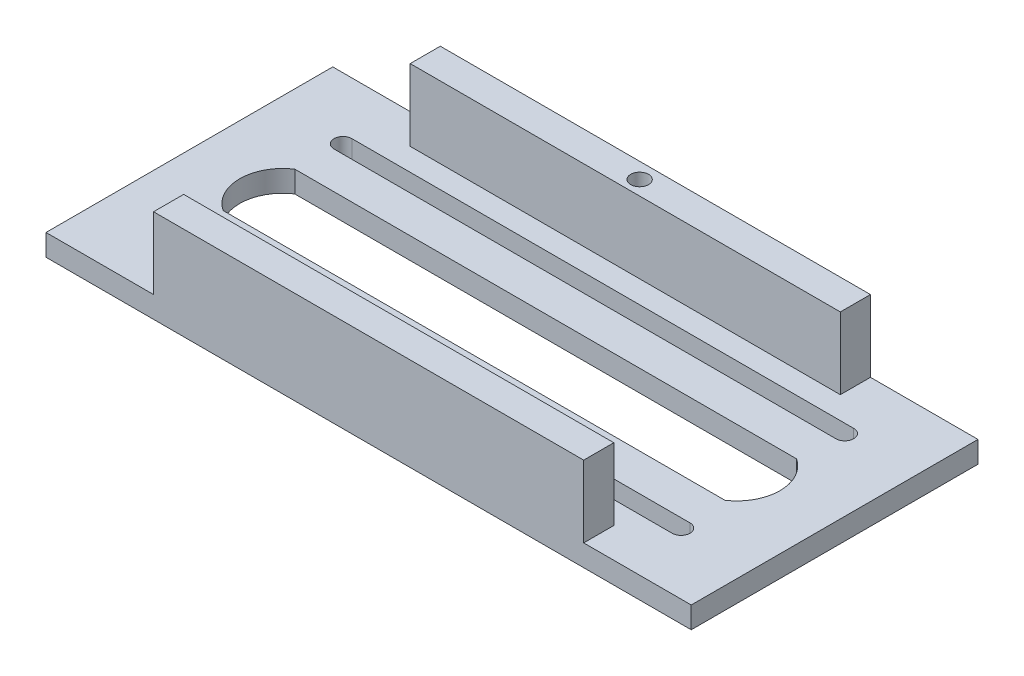
SolidWorks part; units mm, degrees
ref_plane "Front Plane" through (0, 0, 0) normal (0, 0, 1) x (1, 0, 0)
ref_plane "Top Plane" through (0, 0, 0) normal (0, 1, 0) x (1, 0, 0)
ref_plane "Right Plane" through (0, 0, 0) normal (1, 0, 0) x (0, 0, -1)
sketch "Sketch2" plane through (0, 0, 0) normal (0, 1, 0) x (1, 0, 0)
  line L1 (0, 0) -> (228.6, 0)
  line L2 (0, 0) -> (0, 101.6)
  line L3 (0, 101.6) -> (228.6, 101.6)
  line L4 (228.6, 0) -> (228.6, 101.6)
  dimension "D1" = 228.6
  dimension "D2" = 101.6
extrude "Boss-Extrude1" add sketch "Sketch2" along normal blind 7.62
sketch "Sketch3" plane through (0, 7.62, 0) normal (0, 1, 0) x (1, 0, 0)
  line L6 (190.5, 0) -> (38.1, 0)
  line L8 (190.5, 10.668) -> (38.1, 10.668)
  line L10 (0, 101.6) -> (0, 0) construction
  line L23 (190.5, 90.932) -> (38.1, 90.932)
  line L25 (190.5, 101.6) -> (38.1, 101.6)
  line L35 (38.1, 101.6) -> (38.1, 90.932)
  line L36 (38.1, 10.668) -> (38.1, 0)
  line L37 (190.5, 101.6) -> (190.5, 90.932)
  line L38 (190.5, 10.668) -> (190.5, 0)
  line L39 (228.6, 0) -> (228.6, 101.6) construction
  line L40 (228.6, 101.6) -> (0, 101.6) construction
  line L41 (0, 0) -> (228.6, 0) construction
  dimension "D1" = 10.668
  dimension "D2" = 38.1
  dimension "D3" = 38.1
  dimension "D4" = 10.668
extrude "Boss-Extrude2" add sketch "Sketch3" along normal blind 25.4
sketch "Sketch4" plane through (0, 7.62, 0) normal (0, 1, 0) x (1, 0, 0)
  line L0 (25.4, 21.7986) -> (203.2, 21.7986) construction
  line L1 (25.4, 24.9736) -> (203.2, 24.9736)
  line L2 (25.4, 18.6236) -> (203.2, 18.6236)
  line L5 (0, 50.8) -> (228.6, 50.8) construction
  line L6 (0, 101.6) -> (0, 0) construction
  line L7 (228.6, 0) -> (228.6, 101.6) construction
  line L8 (25.4, 79.8014) -> (203.2, 79.8014) construction
  line L9 (25.4, 76.6264) -> (203.2, 76.6264)
  line L10 (25.4, 82.9764) -> (203.2, 82.9764)
  line L16 (190.5, 10.668) -> (38.1, 10.668) construction
  arc A0 (25.4, 24.9736) -> (25.4, 18.6236) centre (25.4, 21.7986) ccw
  arc A1 (203.2, 18.6236) -> (203.2, 24.9736) centre (203.2, 21.7986) ccw
  arc A2 (25.4, 76.6264) -> (25.4, 82.9764) centre (25.4, 79.8014) cw
  arc A3 (203.2, 82.9764) -> (203.2, 76.6264) centre (203.2, 79.8014) cw
  point P2 (114.3, 21.7986)
  point P17 (114.3, 79.8014)
  dimension "D1" = 11.1306
  dimension "D2" = 177.8
  dimension "D3" = 114.3
  dimension "D4" = 6.35
extrude "Cut-Extrude1" cut sketch "Sketch4" against normal through all
sketch "Sketch5" plane through (0, 7.62, 0) normal (0, 1, 0) x (1, 0, 0)
  line L0 (25.4, 18.6236) -> (203.2, 18.6236) construction
  line L1 (24.6329, 63.5) -> (202.4329, 63.5)
  line L3 (24.6329, 38.1) -> (202.4329, 38.1)
  line L4 (38.1, 0) -> (190.5, 0) construction
  arc A0 (24.6329, 63.5) -> (24.6329, 38.1) centre (33.0571, 50.8) ccw
  arc A1 (202.4329, 63.5) -> (202.4329, 38.1) centre (194.0087, 50.8) cw
  point P8 (207.2366, 50.1009)
  point P11 (0, 0)
  point P12 (0, 0)
  dimension "D3" = 15.24
  dimension "D1" = 25.4
  dimension "D2" = 38.1
  dimension "D4" = 0
extrude "Cut-Extrude2" cut sketch "Sketch5" against normal through all
sketch "Sketch6" plane through (0, 0, 0) normal (0, -1, 0) x (1, 0, 0)
  line L0 (0, 0) -> (228.6, 0) construction
  line L1 (228.6, -101.6) -> (0, -101.6) construction
  circle A0 centre (114.3, -96.012) radius 3.175
  point P4 (114.3, 0)
  point P5 (0, 0)
  point P6 (0, 0)
  dimension "D1" = 6.35
  dimension "D2" = 5.588
  dimension "D3" = 0
extrude "Cut-Extrude3" cut sketch "Sketch6" against normal through all
